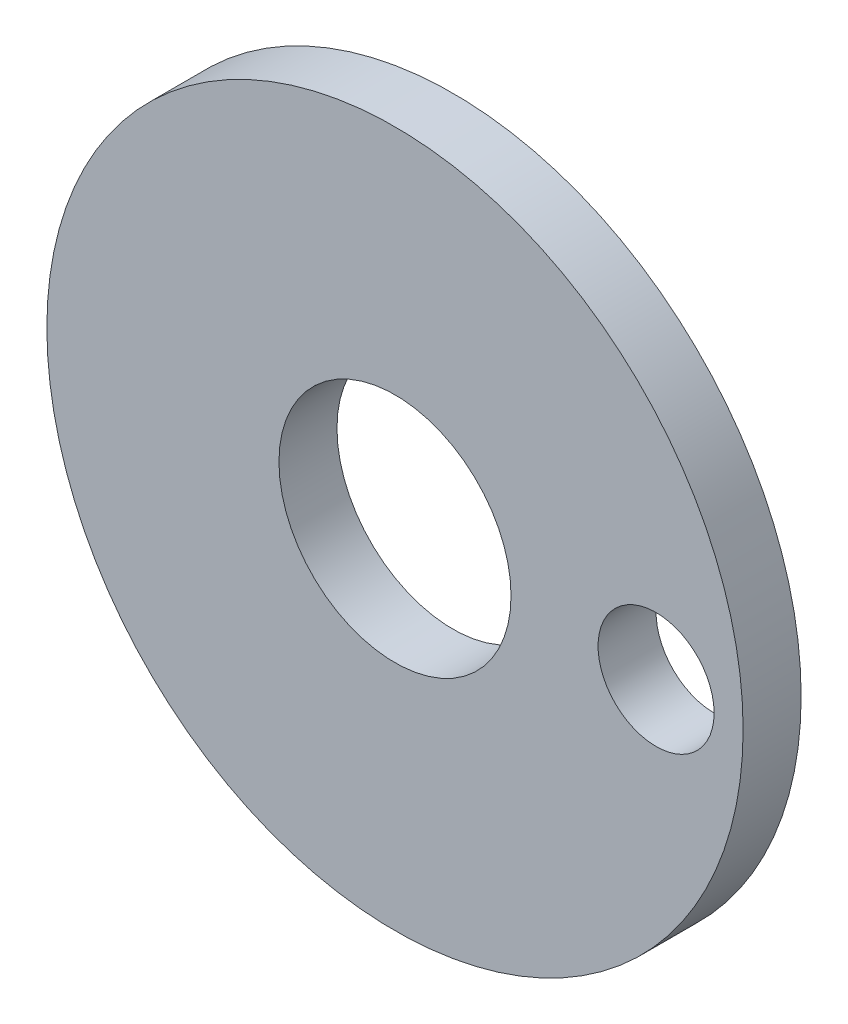
SolidWorks part; units mm, degrees
ref_plane "Front Plane" through (0, 0, 0) normal (0, 0, 1) x (1, 0, 0)
ref_plane "Top Plane" through (0, 0, 0) normal (0, 1, 0) x (1, 0, 0)
ref_plane "Right Plane" through (0, 0, 0) normal (1, 0, 0) x (0, 0, -1)
sketch "Sketch1" plane through (0, 0, 0) normal (0, 0, 1) x (1, 0, 0)
  circle A0 centre (0, 0) radius 6
  circle A1 centre (0, 0) radius 2
  circle A2 centre (4.5, 0) radius 1
  point P6 (6.4245, 0)
  point P7 (2.7931, 0.1642)
  point P8 (0, 0)
  point P9 (0, 0)
  dimension "D1" = 2
  dimension "D2" = 12
  dimension "D3" = 4
  dimension "D4" = 1.5
extrude "Boss-Extrude1" add sketch "Sketch1" along normal blind 1
